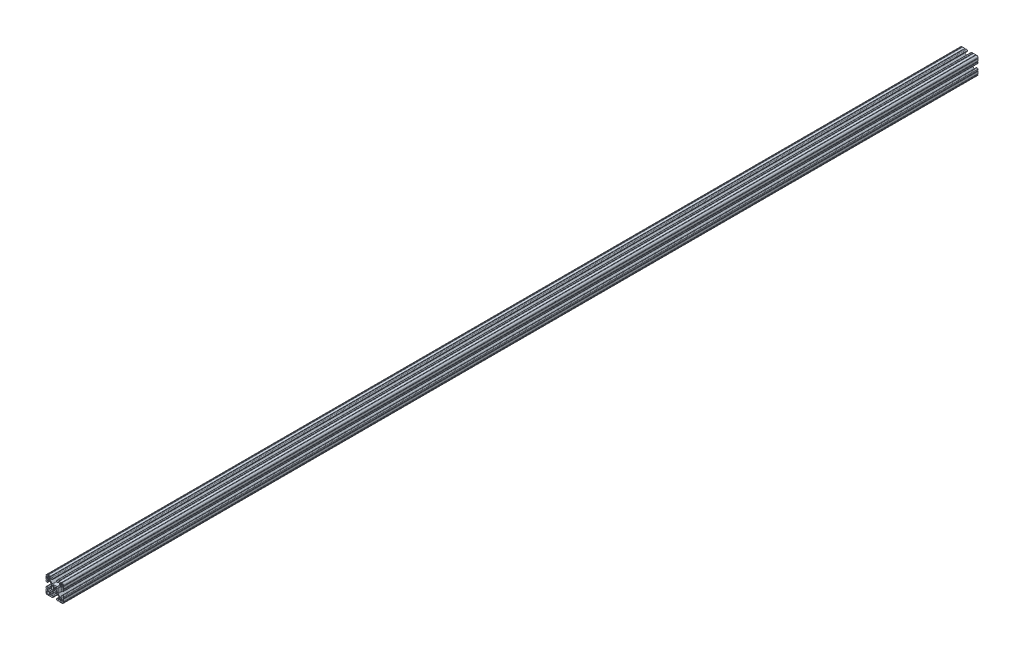
SolidWorks part; units mm, degrees
ref_plane "Front Plane" through (0, 0, 0) normal (0, 0, 1) x (1, 0, 0)
ref_plane "Top Plane" through (0, 0, 0) normal (0, 1, 0) x (1, 0, 0)
ref_plane "Right Plane" through (0, 0, 0) normal (1, 0, 0) x (0, 0, -1)
sketch "Sketch1" plane through (0, 0, 0) normal (0, 0, 1) x (1, 0, 0)
  line L0 (1.5823, 3.1988) -> (3.2921, 4.9085)
  line L1 (3.9207, 5.1689) -> (4.9149, 5.1689)
  line L2 (5.1689, 4.9149) -> (5.1689, 3.9207)
  line L3 (4.9085, 3.2921) -> (3.1988, 1.5823)
  line L4 (3.1988, -1.5823) -> (4.9085, -3.2921)
  line L5 (5.1689, -3.9207) -> (5.1689, -4.9149)
  line L6 (4.9149, -5.1689) -> (3.9207, -5.1689)
  line L7 (3.2921, -4.9085) -> (1.5823, -3.1988)
  line L8 (-1.5823, -3.1988) -> (-3.2921, -4.9085)
  line L9 (-3.9207, -5.1689) -> (-4.9149, -5.1689)
  line L10 (-5.1689, -4.9149) -> (-5.1689, -3.9207)
  line L11 (-4.9085, -3.2921) -> (-3.1988, -1.5823)
  line L12 (-3.1988, 1.5823) -> (-4.9085, 3.2921)
  line L13 (-5.1689, 3.9207) -> (-5.1689, 4.9149)
  line L14 (-4.9149, 5.1689) -> (-3.9207, 5.1689)
  line L15 (-3.2921, 4.9085) -> (-1.5823, 3.1988)
  line L16 (-11.8669, 14.0194) -> (-11.8669, 12.2479)
  line L17 (-12.2479, 11.8669) -> (-14.0195, 11.8669)
  line L18 (-14.0213, 11.8676) -> (-14.5575, 12.4039)
  line L19 (-14.5611, 12.4039) -> (-15.0973, 11.8676)
  line L20 (-15.0991, 11.8669) -> (-16.8707, 11.8669)
  line L21 (-17.2517, 12.2479) -> (-17.2517, 14.4577)
  line L22 (-14.4577, 17.2517) -> (-12.2479, 17.2517)
  line L23 (-11.8669, 16.8707) -> (-11.8669, 15.0991)
  line L24 (-11.8676, 15.0973) -> (-12.4039, 14.5611)
  line L25 (-12.4039, 14.5575) -> (-11.8676, 14.0212)
  line L26 (-14.0194, -11.8669) -> (-12.2479, -11.8669)
  line L27 (-11.8669, -12.2479) -> (-11.8669, -14.0195)
  line L28 (-11.8676, -14.0213) -> (-12.4039, -14.5575)
  line L29 (-12.4039, -14.5611) -> (-11.8676, -15.0973)
  line L30 (-11.8669, -15.0991) -> (-11.8669, -16.8707)
  line L31 (-12.2479, -17.2517) -> (-14.4577, -17.2517)
  line L32 (-17.2517, -14.4577) -> (-17.2517, -12.2479)
  line L33 (-16.8707, -11.8669) -> (-15.0991, -11.8669)
  line L34 (-15.0973, -11.8676) -> (-14.5611, -12.4039)
  line L35 (-14.5575, -12.4039) -> (-14.0212, -11.8676)
  line L36 (11.8669, -14.0194) -> (11.8669, -12.2479)
  line L37 (12.2479, -11.8669) -> (14.0195, -11.8669)
  line L38 (14.0213, -11.8676) -> (14.5575, -12.4039)
  line L39 (14.5611, -12.4039) -> (15.0973, -11.8676)
  line L40 (15.0991, -11.8669) -> (16.8707, -11.8669)
  line L41 (17.2517, -12.2479) -> (17.2517, -14.4577)
  line L42 (14.4577, -17.2517) -> (12.2479, -17.2517)
  line L43 (11.8669, -16.8707) -> (11.8669, -15.0991)
  line L44 (11.8676, -15.0973) -> (12.4039, -14.5611)
  line L45 (12.4039, -14.5575) -> (11.8676, -14.0212)
  line L46 (14.0194, 11.8669) -> (12.2479, 11.8669)
  line L47 (11.8669, 12.2479) -> (11.8669, 14.0195)
  line L48 (11.8676, 14.0213) -> (12.4039, 14.5575)
  line L49 (12.4039, 14.5611) -> (11.8676, 15.0973)
  line L50 (11.8669, 15.0991) -> (11.8669, 16.8707)
  line L51 (12.2479, 17.2517) -> (14.4577, 17.2517)
  line L52 (17.2517, 14.4577) -> (17.2517, 12.2479)
  line L53 (16.8707, 11.8669) -> (15.0991, 11.8669)
  line L54 (15.0973, 11.8676) -> (14.5611, 12.4039)
  line L55 (14.5575, 12.4039) -> (14.0212, 11.8676)
  line L56 (6.3498, -14.9848) -> (5.6531, -14.9848)
  line L57 (4.0778, -16.5601) -> (4.0778, -17.4747)
  line L58 (5.6531, -19.05) -> (7.9756, -19.05)
  line L59 (9.4996, -19.05) -> (14.2981, -19.05)
  line L60 (19.05, -14.3256) -> (19.05, -9.4996)
  line L61 (19.05, -7.9756) -> (19.05, -5.6531)
  line L62 (17.4747, -4.0778) -> (16.5601, -4.0778)
  line L63 (14.9848, -5.6531) -> (14.9848, -6.3498)
  line L64 (15.3661, -6.731) -> (15.6969, -6.731)
  line L65 (16.0782, -7.1122) -> (16.0782, -9.3968)
  line L66 (15.1881, -10.287) -> (12.3526, -10.2871)
  line L67 (11.4535, -9.9142) -> (7.1147, -5.5659)
  line L68 (6.7437, -4.6689) -> (6.7437, 4.6414)
  line L69 (7.1147, 5.5384) -> (11.481, 9.9142)
  line L70 (12.38, 10.2871) -> (15.1881, 10.287)
  line L71 (16.0782, 9.3968) -> (16.0782, 7.1122)
  line L72 (15.6969, 6.731) -> (15.3661, 6.731)
  line L73 (14.9848, 6.3498) -> (14.9848, 5.6531)
  line L74 (16.5601, 4.0778) -> (17.4747, 4.0778)
  line L75 (19.05, 5.6531) -> (19.05, 7.9756)
  line L76 (19.05, 9.4996) -> (19.05, 14.2981)
  line L77 (14.3256, 19.05) -> (9.4996, 19.05)
  line L78 (7.9756, 19.05) -> (5.6531, 19.05)
  line L79 (4.0778, 17.4747) -> (4.0778, 16.5601)
  line L80 (5.6531, 14.9848) -> (6.3498, 14.9848)
  line L81 (6.731, 15.3661) -> (6.731, 15.6969)
  line L82 (7.1122, 16.0782) -> (9.3968, 16.0782)
  line L83 (10.287, 15.1881) -> (10.2871, 12.3526)
  line L84 (9.9142, 11.4535) -> (5.5659, 7.1147)
  line L85 (4.6689, 6.7437) -> (-4.6414, 6.7437)
  line L86 (-5.5384, 7.1147) -> (-9.9142, 11.481)
  line L87 (-10.2871, 12.38) -> (-10.287, 15.1881)
  line L88 (-9.3968, 16.0782) -> (-7.1122, 16.0782)
  line L89 (-6.731, 15.6969) -> (-6.731, 15.3661)
  line L90 (-6.3498, 14.9848) -> (-5.6531, 14.9848)
  line L91 (-4.0778, 16.5601) -> (-4.0778, 17.4747)
  line L92 (-5.6531, 19.05) -> (-7.9756, 19.05)
  line L93 (-9.4996, 19.05) -> (-14.2981, 19.05)
  line L94 (-19.05, 14.3256) -> (-19.05, 9.4996)
  line L95 (-19.05, 7.9756) -> (-19.05, 5.6531)
  line L96 (-17.4747, 4.0778) -> (-16.5601, 4.0778)
  line L97 (-14.9848, 5.6531) -> (-14.9848, 6.3498)
  line L98 (-15.3661, 6.731) -> (-15.6969, 6.731)
  line L99 (-16.0782, 7.1122) -> (-16.0782, 9.3968)
  line L100 (-15.1881, 10.287) -> (-12.3526, 10.2871)
  line L101 (-11.4535, 9.9142) -> (-7.1147, 5.5659)
  line L102 (-6.7437, 4.6689) -> (-6.7437, -4.6414)
  line L103 (-7.1147, -5.5384) -> (-11.481, -9.9142)
  line L104 (-12.38, -10.2871) -> (-15.1881, -10.287)
  line L105 (-16.0782, -9.3968) -> (-16.0782, -7.1122)
  line L106 (-15.6969, -6.731) -> (-15.3661, -6.731)
  line L107 (-14.9848, -6.3498) -> (-14.9848, -5.6531)
  line L108 (-16.5601, -4.0778) -> (-17.4747, -4.0778)
  line L109 (-19.05, -5.6531) -> (-19.05, -7.9756)
  line L110 (-19.05, -9.4996) -> (-19.05, -14.2981)
  line L111 (-14.3256, -19.05) -> (-9.4996, -19.05)
  line L112 (-7.9756, -19.05) -> (-5.6531, -19.05)
  line L113 (-4.0778, -17.4747) -> (-4.0778, -16.5601)
  line L114 (-5.6531, -14.9848) -> (-6.3498, -14.9848)
  line L115 (-6.731, -15.3661) -> (-6.731, -15.6969)
  line L116 (-7.1122, -16.0782) -> (-9.3968, -16.0782)
  line L117 (-10.287, -15.1881) -> (-10.2871, -12.3526)
  line L118 (-9.9142, -11.4535) -> (-5.5659, -7.1147)
  line L119 (-4.6689, -6.7437) -> (4.6414, -6.7437)
  line L120 (5.5384, -7.1147) -> (9.9142, -11.481)
  line L121 (10.2871, -12.38) -> (10.287, -15.1881)
  line L122 (9.3968, -16.0782) -> (7.1122, -16.0782)
  line L123 (6.731, -15.6969) -> (6.731, -15.3661)
  arc A0 (1.178, 3.1119) -> (1.5823, 3.1988) centre (1.3129, 3.4682) ccw
  arc A1 (3.9207, 5.1689) -> (3.2921, 4.9085) centre (3.9207, 4.2799) ccw
  arc A2 (5.1689, 4.9149) -> (4.9149, 5.1689) centre (4.9149, 4.9149) ccw
  arc A3 (4.9085, 3.2921) -> (5.1689, 3.9207) centre (4.2799, 3.9207) ccw
  arc A4 (3.1988, 1.5823) -> (3.1119, 1.178) centre (3.4682, 1.3129) ccw
  arc A5 (3.1119, -1.178) -> (3.1119, 1.178) centre (0, 0) ccw
  arc A6 (3.1119, -1.178) -> (3.1988, -1.5823) centre (3.4682, -1.3129) ccw
  arc A7 (5.1689, -3.9207) -> (4.9085, -3.2921) centre (4.2799, -3.9207) ccw
  arc A8 (4.9149, -5.1689) -> (5.1689, -4.9149) centre (4.9149, -4.9149) ccw
  arc A9 (3.2921, -4.9085) -> (3.9207, -5.1689) centre (3.9207, -4.2799) ccw
  arc A10 (1.5823, -3.1988) -> (1.178, -3.1119) centre (1.3129, -3.4682) ccw
  arc A11 (-1.178, -3.1119) -> (1.178, -3.1119) centre (0, 0) ccw
  arc A12 (-1.178, -3.1119) -> (-1.5823, -3.1988) centre (-1.3129, -3.4682) ccw
  arc A13 (-3.9207, -5.1689) -> (-3.2921, -4.9085) centre (-3.9207, -4.2799) ccw
  arc A14 (-5.1689, -4.9149) -> (-4.9149, -5.1689) centre (-4.9149, -4.9149) ccw
  arc A15 (-4.9085, -3.2921) -> (-5.1689, -3.9207) centre (-4.2799, -3.9207) ccw
  arc A16 (-3.1988, -1.5823) -> (-3.1119, -1.178) centre (-3.4682, -1.3129) ccw
  arc A17 (-3.1119, 1.178) -> (-3.1119, -1.178) centre (0, 0) ccw
  arc A18 (-3.1119, 1.178) -> (-3.1988, 1.5823) centre (-3.4682, 1.3129) ccw
  arc A19 (-5.1689, 3.9207) -> (-4.9085, 3.2921) centre (-4.2799, 3.9207) ccw
  arc A20 (-4.9149, 5.1689) -> (-5.1689, 4.9149) centre (-4.9149, 4.9149) ccw
  arc A21 (-3.2921, 4.9085) -> (-3.9207, 5.1689) centre (-3.9207, 4.2799) ccw
  arc A22 (-1.5823, 3.1988) -> (-1.178, 3.1119) centre (-1.3129, 3.4682) ccw
  arc A23 (1.178, 3.1119) -> (-1.178, 3.1119) centre (0, 0) ccw
  arc A24 (-11.8669, 14.0194) -> (-11.8676, 14.0212) centre (-11.8694, 14.0194) ccw
  arc A25 (-12.2479, 11.8669) -> (-11.8669, 12.2479) centre (-12.2479, 12.2479) ccw
  arc A26 (-14.0213, 11.8676) -> (-14.0195, 11.8669) centre (-14.0195, 11.8694) ccw
  arc A27 (-14.5575, 12.4039) -> (-14.5611, 12.4039) centre (-14.5593, 12.4021) ccw
  arc A28 (-15.0991, 11.8669) -> (-15.0973, 11.8676) centre (-15.0991, 11.8694) ccw
  arc A29 (-17.2517, 12.2479) -> (-16.8707, 11.8669) centre (-16.8707, 12.2479) ccw
  arc A30 (-14.4577, 17.2517) -> (-17.2517, 14.4577) centre (-14.4577, 14.4577) ccw
  arc A31 (-11.8669, 16.8707) -> (-12.2479, 17.2517) centre (-12.2479, 16.8707) ccw
  arc A32 (-11.8676, 15.0973) -> (-11.8669, 15.0991) centre (-11.8694, 15.0991) ccw
  arc A33 (-12.4039, 14.5611) -> (-12.4039, 14.5575) centre (-12.4021, 14.5593) ccw
  arc A34 (-14.0194, -11.8669) -> (-14.0212, -11.8676) centre (-14.0194, -11.8694) ccw
  arc A35 (-11.8669, -12.2479) -> (-12.2479, -11.8669) centre (-12.2479, -12.2479) ccw
  arc A36 (-11.8676, -14.0213) -> (-11.8669, -14.0195) centre (-11.8694, -14.0195) ccw
  arc A37 (-12.4039, -14.5575) -> (-12.4039, -14.5611) centre (-12.4021, -14.5593) ccw
  arc A38 (-11.8669, -15.0991) -> (-11.8676, -15.0973) centre (-11.8694, -15.0991) ccw
  arc A39 (-12.2479, -17.2517) -> (-11.8669, -16.8707) centre (-12.2479, -16.8707) ccw
  arc A40 (-17.2517, -14.4577) -> (-14.4577, -17.2517) centre (-14.4577, -14.4577) ccw
  arc A41 (-16.8707, -11.8669) -> (-17.2517, -12.2479) centre (-16.8707, -12.2479) ccw
  arc A42 (-15.0973, -11.8676) -> (-15.0991, -11.8669) centre (-15.0991, -11.8694) ccw
  arc A43 (-14.5611, -12.4039) -> (-14.5575, -12.4039) centre (-14.5593, -12.4021) ccw
  arc A44 (11.8669, -14.0194) -> (11.8676, -14.0212) centre (11.8694, -14.0194) ccw
  arc A45 (12.2479, -11.8669) -> (11.8669, -12.2479) centre (12.2479, -12.2479) ccw
  arc A46 (14.0213, -11.8676) -> (14.0195, -11.8669) centre (14.0195, -11.8694) ccw
  arc A47 (14.5575, -12.4039) -> (14.5611, -12.4039) centre (14.5593, -12.4021) ccw
  arc A48 (15.0991, -11.8669) -> (15.0973, -11.8676) centre (15.0991, -11.8694) ccw
  arc A49 (17.2517, -12.2479) -> (16.8707, -11.8669) centre (16.8707, -12.2479) ccw
  arc A50 (14.4577, -17.2517) -> (17.2517, -14.4577) centre (14.4577, -14.4577) ccw
  arc A51 (11.8669, -16.8707) -> (12.2479, -17.2517) centre (12.2479, -16.8707) ccw
  arc A52 (11.8676, -15.0973) -> (11.8669, -15.0991) centre (11.8694, -15.0991) ccw
  arc A53 (12.4039, -14.5611) -> (12.4039, -14.5575) centre (12.4021, -14.5593) ccw
  arc A54 (14.0194, 11.8669) -> (14.0212, 11.8676) centre (14.0194, 11.8694) ccw
  arc A55 (11.8669, 12.2479) -> (12.2479, 11.8669) centre (12.2479, 12.2479) ccw
  arc A56 (11.8676, 14.0213) -> (11.8669, 14.0195) centre (11.8694, 14.0195) ccw
  arc A57 (12.4039, 14.5575) -> (12.4039, 14.5611) centre (12.4021, 14.5593) ccw
  arc A58 (11.8669, 15.0991) -> (11.8676, 15.0973) centre (11.8694, 15.0991) ccw
  arc A59 (12.2479, 17.2517) -> (11.8669, 16.8707) centre (12.2479, 16.8707) ccw
  arc A60 (17.2517, 14.4577) -> (14.4577, 17.2517) centre (14.4577, 14.4577) ccw
  arc A61 (16.8707, 11.8669) -> (17.2517, 12.2479) centre (16.8707, 12.2479) ccw
  arc A62 (15.0973, 11.8676) -> (15.0991, 11.8669) centre (15.0991, 11.8694) ccw
  arc A63 (14.5611, 12.4039) -> (14.5575, 12.4039) centre (14.5593, 12.4021) ccw
  arc A64 (6.731, -15.3661) -> (6.3498, -14.9848) centre (6.35, -15.3658) ccw
  arc A65 (5.6531, -14.9848) -> (4.0778, -16.5601) centre (5.6526, -16.5596) ccw
  arc A66 (4.0778, -17.4747) -> (5.6531, -19.05) centre (5.6526, -17.4752) ccw
  arc A67 (9.4996, -19.05) -> (7.9756, -19.05) centre (8.7376, -19.05) ccw
  arc A68 (15.8221, -19.0496) -> (14.2981, -19.05) centre (15.0601, -19.05) ccw
  arc A69 (15.8221, -19.0496) -> (19.0499, -15.8496) centre (15.875, -15.875) ccw
  arc A70 (19.05, -14.3256) -> (19.0499, -15.8496) centre (19.05, -15.0876) ccw
  arc A71 (19.05, -7.9756) -> (19.05, -9.4996) centre (19.05, -8.7376) ccw
  arc A72 (19.05, -5.6531) -> (17.4747, -4.0778) centre (17.4752, -5.6526) ccw
  arc A73 (16.5601, -4.0778) -> (14.9848, -5.6531) centre (16.5596, -5.6526) ccw
  arc A74 (14.9848, -6.3498) -> (15.3661, -6.731) centre (15.3658, -6.35) ccw
  arc A75 (16.0782, -7.1122) -> (15.6969, -6.731) centre (15.6972, -7.112) ccw
  arc A76 (15.1881, -10.287) -> (16.0782, -9.3968) centre (15.1892, -9.398) ccw
  arc A77 (11.4535, -9.9142) -> (12.3526, -10.2871) centre (12.3525, -9.0171) ccw
  arc A78 (6.7437, -4.6689) -> (7.1147, -5.5659) centre (8.0137, -4.6689) ccw
  arc A79 (7.1147, 5.5384) -> (6.7437, 4.6414) centre (8.0137, 4.6414) ccw
  arc A80 (12.38, 10.2871) -> (11.481, 9.9142) centre (12.38, 9.0171) ccw
  arc A81 (16.0782, 9.3968) -> (15.1881, 10.287) centre (15.1892, 9.398) ccw
  arc A82 (15.6969, 6.731) -> (16.0782, 7.1122) centre (15.6972, 7.112) ccw
  arc A83 (15.3661, 6.731) -> (14.9848, 6.3498) centre (15.3658, 6.35) ccw
  arc A84 (14.9848, 5.6531) -> (16.5601, 4.0778) centre (16.5596, 5.6526) ccw
  arc A85 (17.4747, 4.0778) -> (19.05, 5.6531) centre (17.4752, 5.6526) ccw
  arc A86 (19.05, 9.4996) -> (19.05, 7.9756) centre (19.05, 8.7376) ccw
  arc A87 (19.0496, 15.8221) -> (19.05, 14.2981) centre (19.05, 15.0601) ccw
  arc A88 (19.0496, 15.8221) -> (15.8496, 19.0499) centre (15.875, 15.875) ccw
  arc A89 (14.3256, 19.05) -> (15.8496, 19.0499) centre (15.0876, 19.05) ccw
  arc A90 (7.9756, 19.05) -> (9.4996, 19.05) centre (8.7376, 19.05) ccw
  arc A91 (5.6531, 19.05) -> (4.0778, 17.4747) centre (5.6526, 17.4752) ccw
  arc A92 (4.0778, 16.5601) -> (5.6531, 14.9848) centre (5.6526, 16.5596) ccw
  arc A93 (6.3498, 14.9848) -> (6.731, 15.3661) centre (6.35, 15.3658) ccw
  arc A94 (7.1122, 16.0782) -> (6.731, 15.6969) centre (7.112, 15.6972) ccw
  arc A95 (10.287, 15.1881) -> (9.3968, 16.0782) centre (9.398, 15.1892) ccw
  arc A96 (9.9142, 11.4535) -> (10.2871, 12.3526) centre (9.0171, 12.3525) ccw
  arc A97 (4.6689, 6.7437) -> (5.5659, 7.1147) centre (4.6689, 8.0137) ccw
  arc A98 (-5.5384, 7.1147) -> (-4.6414, 6.7437) centre (-4.6414, 8.0137) ccw
  arc A99 (-10.2871, 12.38) -> (-9.9142, 11.481) centre (-9.0171, 12.38) ccw
  arc A100 (-9.3968, 16.0782) -> (-10.287, 15.1881) centre (-9.398, 15.1892) ccw
  arc A101 (-6.731, 15.6969) -> (-7.1122, 16.0782) centre (-7.112, 15.6972) ccw
  arc A102 (-6.731, 15.3661) -> (-6.3498, 14.9848) centre (-6.35, 15.3658) ccw
  arc A103 (-5.6531, 14.9848) -> (-4.0778, 16.5601) centre (-5.6526, 16.5596) ccw
  arc A104 (-4.0778, 17.4747) -> (-5.6531, 19.05) centre (-5.6526, 17.4752) ccw
  arc A105 (-9.4996, 19.05) -> (-7.9756, 19.05) centre (-8.7376, 19.05) ccw
  arc A106 (-15.8221, 19.0496) -> (-14.2981, 19.05) centre (-15.0601, 19.05) ccw
  arc A107 (-15.8221, 19.0496) -> (-19.0499, 15.8496) centre (-15.875, 15.875) ccw
  arc A108 (-19.05, 14.3256) -> (-19.0499, 15.8496) centre (-19.05, 15.0876) ccw
  arc A109 (-19.05, 7.9756) -> (-19.05, 9.4996) centre (-19.05, 8.7376) ccw
  arc A110 (-19.05, 5.6531) -> (-17.4747, 4.0778) centre (-17.4752, 5.6526) ccw
  arc A111 (-16.5601, 4.0778) -> (-14.9848, 5.6531) centre (-16.5596, 5.6526) ccw
  arc A112 (-14.9848, 6.3498) -> (-15.3661, 6.731) centre (-15.3658, 6.35) ccw
  arc A113 (-16.0782, 7.1122) -> (-15.6969, 6.731) centre (-15.6972, 7.112) ccw
  arc A114 (-15.1881, 10.287) -> (-16.0782, 9.3968) centre (-15.1892, 9.398) ccw
  arc A115 (-11.4535, 9.9142) -> (-12.3526, 10.2871) centre (-12.3525, 9.0171) ccw
  arc A116 (-6.7437, 4.6689) -> (-7.1147, 5.5659) centre (-8.0137, 4.6689) ccw
  arc A117 (-7.1147, -5.5384) -> (-6.7437, -4.6414) centre (-8.0137, -4.6414) ccw
  arc A118 (-12.38, -10.2871) -> (-11.481, -9.9142) centre (-12.38, -9.0171) ccw
  arc A119 (-16.0782, -9.3968) -> (-15.1881, -10.287) centre (-15.1892, -9.398) ccw
  arc A120 (-15.6969, -6.731) -> (-16.0782, -7.1122) centre (-15.6972, -7.112) ccw
  arc A121 (-15.3661, -6.731) -> (-14.9848, -6.3498) centre (-15.3658, -6.35) ccw
  arc A122 (-14.9848, -5.6531) -> (-16.5601, -4.0778) centre (-16.5596, -5.6526) ccw
  arc A123 (-17.4747, -4.0778) -> (-19.05, -5.6531) centre (-17.4752, -5.6526) ccw
  arc A124 (-19.05, -9.4996) -> (-19.05, -7.9756) centre (-19.05, -8.7376) ccw
  arc A125 (-19.0496, -15.8221) -> (-19.05, -14.2981) centre (-19.05, -15.0601) ccw
  arc A126 (-19.0496, -15.8221) -> (-15.8496, -19.0499) centre (-15.875, -15.875) ccw
  arc A127 (-14.3256, -19.05) -> (-15.8496, -19.0499) centre (-15.0876, -19.05) ccw
  arc A128 (-7.9756, -19.05) -> (-9.4996, -19.05) centre (-8.7376, -19.05) ccw
  arc A129 (-5.6531, -19.05) -> (-4.0778, -17.4747) centre (-5.6526, -17.4752) ccw
  arc A130 (-4.0778, -16.5601) -> (-5.6531, -14.9848) centre (-5.6526, -16.5596) ccw
  arc A131 (-6.3498, -14.9848) -> (-6.731, -15.3661) centre (-6.35, -15.3658) ccw
  arc A132 (-7.1122, -16.0782) -> (-6.731, -15.6969) centre (-7.112, -15.6972) ccw
  arc A133 (-10.287, -15.1881) -> (-9.3968, -16.0782) centre (-9.398, -15.1892) ccw
  arc A134 (-9.9142, -11.4535) -> (-10.2871, -12.3526) centre (-9.0171, -12.3525) ccw
  arc A135 (-4.6689, -6.7437) -> (-5.5659, -7.1147) centre (-4.6689, -8.0137) ccw
  arc A136 (5.5384, -7.1147) -> (4.6414, -6.7437) centre (4.6414, -8.0137) ccw
  arc A137 (10.2871, -12.38) -> (9.9142, -11.481) centre (9.0171, -12.38) ccw
  arc A138 (9.3968, -16.0782) -> (10.287, -15.1881) centre (9.398, -15.1892) ccw
  arc A139 (6.731, -15.6969) -> (7.1122, -16.0782) centre (7.112, -15.6972) ccw
extrude "Extrude1" add sketch "Sketch1" against normal blind 1981.2
